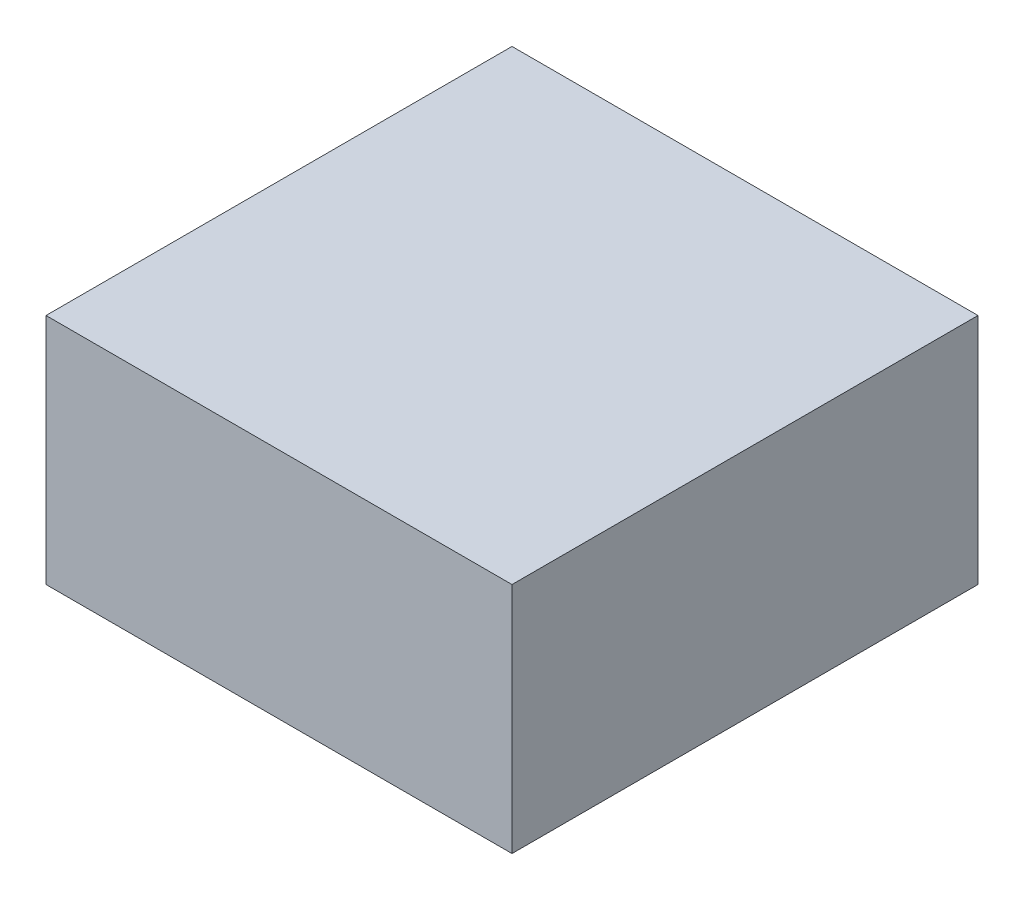
SolidWorks part; units mm, degrees
ref_plane "Front Plane" through (0, 0, 0) normal (0, 0, 1) x (1, 0, 0)
ref_plane "Top Plane" through (0, 0, 0) normal (0, 1, 0) x (1, 0, 0)
ref_plane "Right Plane" through (0, 0, 0) normal (1, 0, 0) x (0, 0, -1)
sketch "Sketch1" plane through (0, 0, 0) normal (0, 0, 1) x (1, 0, 0)
  line L1 (50, -25) -> (-50, -25)
  line L2 (50, -25) -> (50, 25)
  line L3 (50, 25) -> (-50, 25)
  line L4 (-50, -25) -> (-50, 25)
  line L5 (50, -25) -> (-50, 25) construction
  line L6 (50, 25) -> (-50, -25) construction
  point P0 (0, 0)
  dimension "D1" = 100
  dimension "D2" = 50
extrude "Boss-Extrude1" add sketch "Sketch1" along normal blind 100
